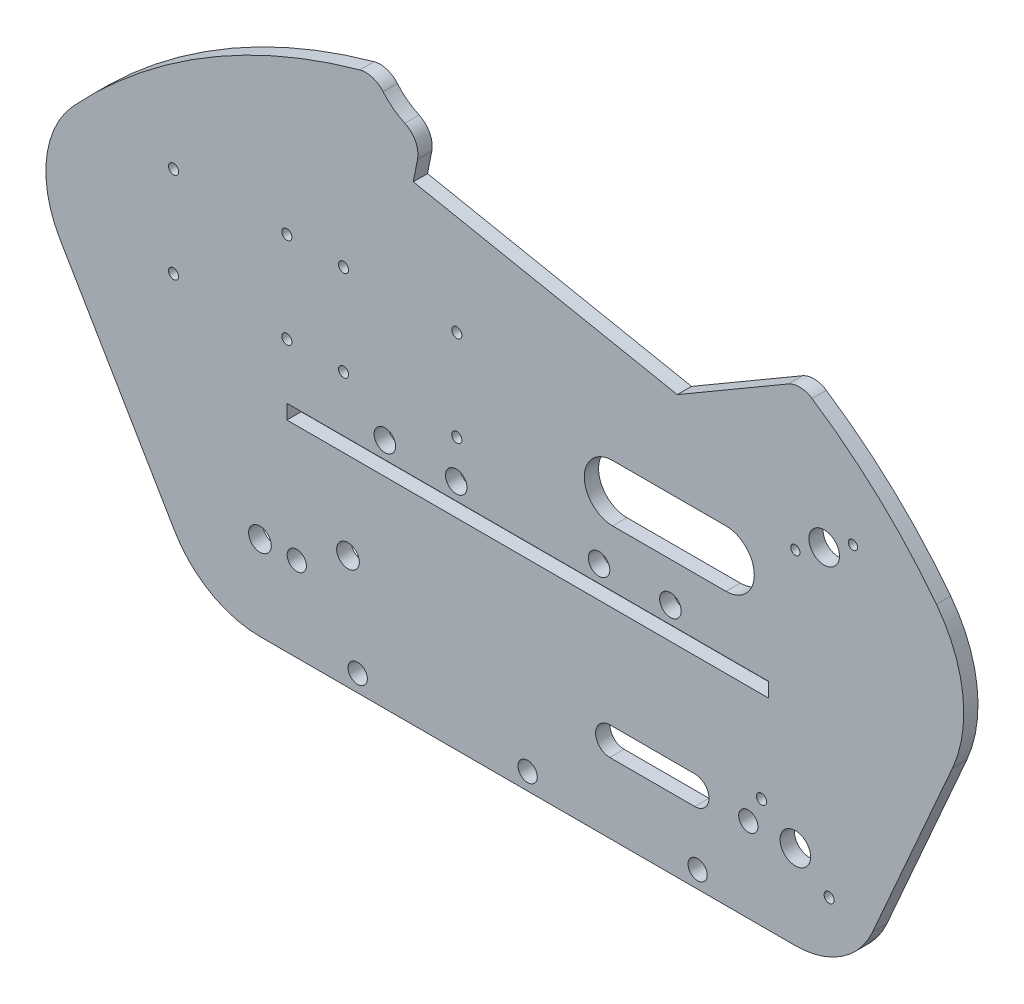
SolidWorks part; units mm, degrees
ref_plane "Front Plane" through (0, 0, 0) normal (0, 0, 1) x (1, 0, 0)
ref_plane "Top Plane" through (0, 0, 0) normal (0, 1, 0) x (1, 0, 0)
ref_plane "Right Plane" through (0, 0, 0) normal (1, 0, 0) x (0, 0, -1)
sketch "Sketch1" plane through (0, 0, 0) normal (0, 0, 1) x (1, 0, 0)
  line L8 (0, 18.9078) -> (120.015, 18.9078) construction
  line L18 (155.2575, 52.1157) -> (-35.2425, 52.1157) construction
  line L37 (0, 0) -> (120.015, 0)
  line L42 (19.7347, 25.5664) -> (0, 18.9078) construction
  line L54 (155.2575, 52.1157) -> (137.3256, 11.3022)
  line L55 (60.0075, 52.1157) -> (60.0075, 18.9078) construction
  line L56 (-35.2425, 52.1157) -> (-17.3106, 11.3022)
  line L59 (151.631, 82.096) -> (-31.616, 82.096) construction
  circle A21 centre (120.015, 18.9078) radius 3.429
  circle A22 centre (0, 18.9078) radius 2.54
  circle A24 centre (19.7347, 25.5664) radius 2.54
  arc A25 (137.3256, 11.3022) -> (120.015, 0) centre (120.015, 18.9078) cw
  arc A26 (0, 0) -> (-17.3106, 11.3022) centre (0, 18.9078) cw
  arc A28 (151.631, 82.096) -> (-31.616, 82.096) centre (60.0075, 11.7572) ccw
  arc A29 (151.631, 82.096) -> (155.2575, 52.1157) centre (128.1135, 64.0417) cw
  arc A30 (-31.616, 82.096) -> (-35.2425, 52.1157) centre (-8.0985, 64.0417) ccw
  dimension "D5" = 18.9078
  dimension "D8" = 29.9803
  dimension "D3" = 52.1157
  dimension "D2" = 6.858
  dimension "D10" = 5.08
  dimension "D1" = 190.5
  dimension "D4" = 18.645
  dimension "D6" = 20.8278
  dimension "D7" = 120.015
  dimension "D9" = 183.2469
extrude "Boss-Extrude1" add sketch "Sketch1" along normal blind 3.2004
sketch "Sketch2" plane through (0, 0, 0) normal (0, 0, -1) x (-1, 0, 0)
  line L14 (-155.2575, 52.1157) -> (35.2425, 52.1157) construction
  line L28 (-92.0115, 52.1157) -> (-76.0095, 52.1157) construction
  line L29 (-76.0095, 52.1157) -> (-44.0055, 52.1157) construction
  line L30 (-44.0055, 52.1157) -> (-28.0035, 52.1157) construction
  circle A0 centre (-92.0115, 52.1157) radius 2.413
  circle A1 centre (-76.0095, 52.1157) radius 2.413
  circle A2 centre (-44.0055, 52.1157) radius 2.413
  circle A3 centre (-28.0035, 52.1157) radius 2.413
  point P11 (-36.0045, 52.1157)
  point P16 (-84.0105, 52.1157)
  dimension "D3" = 4.826
  dimension "D2" = 16.002
  dimension "D4" = 48.006
extrude "Cut-Extrude1" cut sketch "Sketch2" against normal blind 3.2004
sketch "Sketch3" plane through (0, 0, 3.2004) normal (0, 0, 1) x (1, 0, 0)
  line L0 (60.0075, 7.62) -> (60.0075, 0) construction
  line L1 (21.9075, 3.81) -> (98.1075, 3.81) construction
  line L2 (0, 0) -> (120.015, 0) construction
  circle A0 centre (21.9075, 3.81) radius 2.159
  circle A1 centre (60.0075, 3.81) radius 2.159
  circle A2 centre (98.1075, 3.81) radius 2.159
  point P6 (60.0075, 3.81)
  dimension "D3" = 4.318
  dimension "D1" = 76.2
  dimension "D2" = 7.62
extrude "Cut-Extrude2" cut sketch "Sketch3" against normal up to surface (3.2004 mm away) up to face at (89.5985, 52.1157, 0)
sketch "Sketch5" plane through (0, 0, 0) normal (0, 0, -1) x (-1, 0, 0)
  line L0 (-60.0075, 52.1157) -> (-60.0075, 0) construction
  line L1 (-76.0095, 52.1157) -> (-44.0055, 52.1157) construction
  line L3 (0, 0) -> (-120.015, 0) construction
sketch "Sketch6" plane through (0, 0, 0) normal (0, 0, -1) x (-1, 0, 0)
  line L0 (-155.2575, 52.1157) -> (35.2425, 52.1157) construction
  line L1 (-113.9825, 81.3257) -> (-6.0325, 81.3257) construction
  line L2 (-113.9825, 81.3257) -> (-113.9825, 55.9257) construction
  line L3 (-113.9825, 55.9257) -> (-6.0325, 55.9257) construction
  line L4 (-6.0325, 81.3257) -> (-6.0325, 55.9257) construction
  line L5 (-60.0075, 52.1157) -> (-60.0075, 18.9078) construction
  line L6 (-60.0075, 55.9257) -> (-60.0075, 52.1157) construction
  line L7 (-60.0075, 52.1157) -> (-60.0075, 48.3057) construction
  line L9 (-6.0325, 48.3057) -> (-113.9825, 48.3057)
  line L10 (-6.0325, 48.3057) -> (-6.0325, 45.0545)
  line L11 (-6.0325, 45.0545) -> (-113.9825, 45.0545)
  line L12 (-113.9825, 48.3057) -> (-113.9825, 45.0545)
  dimension "D1" = 25.4
  dimension "D2" = 107.95
  dimension "D3" = 3.81
  dimension "D4" = 7.62
  dimension "D5" = 3.2512
extrude "Cut-Extrude3" cut sketch "Sketch6" against normal up to surface (3.2004 mm away) up to face at (24.0665, 3.81, 3.2004)
sketch "Sketch7" plane through (0, 0, 3.2004) normal (0, 0, 1) x (1, 0, 0)
  line L0 (146.2916, 31.7089) -> (111.6995, 46.9073) construction
  line L1 (111.6995, 46.9073) -> (126.4745, 80.5358) construction
  line L3 (137.3256, 11.3022) -> (155.2575, 52.1157) construction
  circle A0 centre (126.4745, 80.5358) radius 3.429
  circle A3 centre (120.015, 18.9078) radius 3.429 construction
  dimension "D1" = 37.7837
  dimension "D2" = 36.7311
extrude "Cut-Extrude4" cut sketch "Sketch7" against normal up to surface (3.2004 mm away) up to face at (60.0075, 46.6801, 0)
sketch "Sketch8" plane through (0, 0, 3.2004) normal (0, 0, 1) x (1, 0, 0)
  line L0 (-32.6149, 80.7753) -> (-17.2714, 56.9367)
  line L1 (-17.2714, 56.9367) -> (38.7942, 93.0228)
  line L2 (38.7942, 93.0228) -> (47.3024, 126.5656)
  line L3 (0, 18.9078) -> (0, 56.9367) construction
  line L4 (0, 56.9367) -> (-17.2714, 56.9367) construction
  line L5 (0, 0) -> (120.015, 0) construction
  arc A0 (151.631, 82.096) -> (-31.616, 82.096) centre (60.0075, 11.7572) ccw construction
  arc A1 (47.3024, 126.5656) -> (-32.6149, 80.7753) centre (60.0075, 11.7572) ccw
  circle A2 centre (0, 18.9078) radius 2.54 construction
  dimension "D1" = 66.675
  dimension "D2" = 137
  dimension "D3" = 28.3497
  dimension "D4" = 38.0289
  dimension "D5" = 17.2714
sketch "Sketch9" plane through (0, 0, 3.2004) normal (0, 0, 1) x (1, 0, 0)
  line L1 (-37.7469, 127.2665) -> (113.9825, 127.2665)
  line L2 (-37.7469, 127.2665) -> (-37.7469, 55.9257)
  line L3 (-37.7469, 55.9257) -> (113.9825, 55.9257)
  line L4 (113.9825, 127.2665) -> (113.9825, 55.9257)
  line L6 (113.9825, 81.3257) -> (113.9825, 55.9257) construction
  line L7 (113.9825, 55.9257) -> (6.0325, 55.9257) construction
  arc A0 (151.631, 82.096) -> (-31.616, 82.096) centre (60.0075, 11.7572) ccw construction
  arc A1 (-31.616, 82.096) -> (-35.2425, 52.1157) centre (-8.0985, 64.0417) ccw construction
sketch "Sketch11" plane through (0, 0, 3.2004) normal (0, 0, 1) x (1, 0, 0)
  line L0 (121.0825, 109.7993) -> (93.5384, 93.7342)
  line L1 (93.5384, 93.7342) -> (34.363, 105.4552)
  line L2 (34.363, 105.4552) -> (38.2746, 125.2036)
  line L6 (113.9825, 48.3057) -> (6.0325, 48.3057) construction
  arc A0 (151.631, 82.096) -> (-31.616, 82.096) centre (60.0075, 11.7572) ccw construction
  arc A1 (38.2746, 125.2036) -> (121.0825, 109.7993) centre (60.0075, 11.7572) cw
  point P4 (0, 0)
  point P5 (0, 0)
  point P6 (0, 0)
  point P7 (0, 0)
  point P10 (0, 0)
  dimension "D1" = 60.325
  dimension "D2" = 20.1321
  dimension "D3" = 11.204
  dimension "D4" = 41.2393
  dimension "D5" = 84.2284
extrude "Cut-Extrude5" cut sketch "Sketch11" against normal up to surface (3.2004 mm away) up to face at (123.0455, 80.5358, 0)
sketch "Sketch12" plane through (0, 0, 3.2004) normal (0, 0, 1) x (1, 0, 0)
  line L2 (35.6411, 114.8543) -> (36.2027, 114.7431)
  line L3 (38.2746, 125.2036) -> (34.363, 105.4552) construction
  line L4 (38.2746, 125.2036) -> (36.2027, 114.7431)
  arc A0 (25.8777, 122.1092) -> (35.6411, 114.8543) centre (38.3949, 128.7574) ccw
  arc A2 (38.2746, 125.2036) -> (-31.616, 82.096) centre (60.0075, 11.7572) ccw construction
  arc A3 (25.8777, 122.1092) -> (38.2746, 125.2036) centre (60.0075, 11.7572) cw
  dimension "D1" = 0.5725
  dimension "D3" = 14.1732
  dimension "D2" = 10.6637
extrude "Cut-Extrude6" cut sketch "Sketch12" against normal up to surface (3.2004 mm away) up to face at (63.7171, 60.738, 0)
sketch "Sketch14" plane through (0, 0, 3.2004) normal (0, 0, 1) x (1, 0, 0)
  line L0 (-44.8116, 54.6857) -> (-19.1425, 10.9597)
  line L1 (0, 0) -> (120.015, 0) construction
  line L2 (-41.8599, 82.0446) -> (25.8777, 122.1092) construction
  line L3 (-41.8599, 82.0446) -> (-44.8116, 54.6857) construction
  line L4 (-9.8103, 145.4597) -> (-9.8103, -20.3847) construction
  arc A0 (25.8777, 122.1092) -> (-41.8599, 82.0446) centre (58.921, -11.052) ccw
  arc A1 (-41.8599, 82.0446) -> (-44.8116, 54.6857) centre (-24.8979, 66.3759) ccw
  arc A4 (-19.1425, 10.9597) -> (0, 0) centre (0, 22.1972) ccw
  arc A5 (25.8777, 122.1092) -> (0, 0) centre (72.988, 48.3288) ccw
  dimension "D2" = 137.1997
  dimension "D4" = 87.5381
  dimension "D5" = 23.0914
  dimension "D1" = 30.415
  dimension "D3" = 78.6991
  dimension "D6" = 27.5176
extrude "Boss-Extrude2" add sketch "Sketch14" against normal up to surface (3.2004 mm away) up to face at (58.8634, 68.0215, 0)
sketch "Sketch13" plane through (0, 0, 3.2004) normal (0, 0, 1) x (1, 0, 0)
  line L0 (44.1325, 81.0717) -> (44.1325, 60.7517) construction
  line L5 (18.7325, 81.0717) -> (18.7325, 60.7517) construction
  line L6 (44.1325, 70.9117) -> (18.7325, 70.9117) construction
  line L7 (6.0325, 81.0717) -> (6.0325, 60.7517) construction
  line L8 (-19.3675, 81.0717) -> (-19.3675, 60.7517) construction
  line L9 (6.0325, 70.9117) -> (-19.3675, 70.9117) construction
  line L10 (113.9825, 48.3057) -> (6.0325, 48.3057) construction
  line L11 (113.9825, 45.0545) -> (113.9825, 48.3057) construction
  circle A0 centre (44.1325, 81.0717) radius 1.1303
  circle A1 centre (44.1325, 60.7517) radius 1.1303
  circle A2 centre (18.7325, 60.7517) radius 1.1303
  circle A3 centre (18.7325, 81.0717) radius 1.1303
  circle A4 centre (6.0325, 81.0717) radius 1.1303
  circle A5 centre (6.0325, 60.7517) radius 1.1303
  circle A6 centre (-19.3675, 60.7517) radius 1.1303
  circle A7 centre (-19.3675, 81.0717) radius 1.1303
  point P13 (31.4325, 70.9117)
  point P22 (-6.6675, 70.9117)
  dimension "D5" = 2.2606
  dimension "D1" = 69.85
  dimension "D2" = 12.7
  dimension "D3" = 25.4
  dimension "D4" = 20.32
  dimension "D6" = 22.606
extrude "Cut-Extrude7" cut sketch "Sketch13" against normal up to surface (3.2004 mm away) up to face at (57.3158, 68.214, 0)
sketch "Sketch15" plane through (0, 0, 3.2004) normal (0, 0, 1) x (1, 0, 0)
  line L0 (113.9825, 48.3057) -> (6.0325, 48.3057) construction
  line L1 (79.0575, 73.7057) -> (104.4575, 73.7057)
  line L2 (79.0575, 73.7057) -> (79.0575, 61.0057) construction
  line L3 (79.0575, 61.0057) -> (104.4575, 61.0057)
  line L4 (104.4575, 73.7057) -> (104.4575, 61.0057) construction
  line L5 (113.9825, 45.0545) -> (113.9825, 48.3057) construction
  line L6 (78.4225, 22.0828) -> (97.4725, 22.0828)
  line L7 (78.4225, 22.0828) -> (78.4225, 15.7328) construction
  line L8 (78.4225, 15.7328) -> (97.4725, 15.7328)
  line L9 (97.4725, 22.0828) -> (97.4725, 15.7328) construction
  line L10 (6.0325, 45.0545) -> (113.9825, 45.0545) construction
  line L11 (97.4725, 18.9078) -> (120.015, 18.9078) construction
  line L12 (0, 0) -> (120.015, 0) construction
  arc A0 (104.4575, 73.7057) -> (104.4575, 61.0057) centre (104.4575, 67.3557) cw
  arc A1 (79.0575, 73.7057) -> (79.0575, 61.0057) centre (79.0575, 67.3557) ccw
  arc A2 (97.4725, 22.0828) -> (97.4725, 15.7328) centre (97.4725, 18.9078) cw
  arc A3 (78.4225, 22.0828) -> (78.4225, 15.7328) centre (78.4225, 18.9078) ccw
  circle A4 centre (120.015, 18.9078) radius 3.429 construction
  circle A5 centre (92.0115, 52.1157) radius 2.413 construction
  dimension "D4" = 8.89
  dimension "D1" = 25.4
  dimension "D2" = 12.7
  dimension "D3" = 12.446
  dimension "D5" = 6.35
  dimension "D6" = 19.05
  dimension "D7" = 16.51
extrude "Cut-Extrude8" cut sketch "Sketch15" against normal up to surface (3.2004 mm away) up to face at (43.0022, 60.7517, 0)
fillet "Fillet1" radius 5.08 3 edges at (121.0825, 109.7993, 1.6002) (36.2027, 114.7431, 1.6002) (25.8777, 122.1092, 1.6002)
sketch "Sketch16" plane through (0, 0, 3.2004) normal (0, 0, 1) x (1, 0, 0)
  line L0 (112.4381, 24.6798) -> (127.5919, 13.1357) construction
  line L1 (0, 0) -> (120.015, 0) construction
  line L2 (120.0293, 76.8147) -> (132.9196, 84.2569) construction
  line L4 (111.6995, 46.9073) -> (126.4745, 80.5358) construction
  circle A0 centre (112.4381, 24.6798) radius 1.1303
  circle A1 centre (127.5919, 13.1357) radius 1.1303
  circle A2 centre (120.0293, 76.8147) radius 1.025
  circle A3 centre (132.9196, 84.2569) radius 1.025
  circle A4 centre (120.015, 18.9078) radius 3.429 construction
  circle A5 centre (126.4745, 80.5358) radius 3.429 construction
  point P10 (120.015, 18.9078)
  point P17 (126.4745, 80.5358)
  dimension "D1" = 2.2606
  dimension "D4" = 2.05
  dimension "D2" = 37.3
  dimension "D3" = 19.05
  dimension "D5" = 14.8844
  dimension "D6" = 36.281
extrude "Cut-Extrude9" cut sketch "Sketch16" against normal up to surface (3.2004 mm away) up to face at (87.9475, 18.9078, 0)
sketch "Sketch20" plane through (0, 0, 3.2004) normal (0, 0, 1) x (1, 0, 0)
  line L0 (8.255, 18.9078) -> (109.4765, 18.9078) construction
  line L1 (60.0075, 18.9078) -> (60.0075, 0) construction
  line L3 (0, 0) -> (120.015, 0) construction
  circle A0 centre (8.255, 18.9078) radius 2.159
  circle A1 centre (109.4765, 18.9078) radius 2.159
  circle A3 centre (0, 18.9078) radius 2.54 construction
  circle A4 centre (120.015, 18.9078) radius 3.429 construction
  dimension "D1" = 4.318
  dimension "D3" = 10.5385
  dimension "D2" = 8.255
  dimension "D4" = 18.9078
extrude "Cut-Extrude11" cut sketch "Sketch20" against normal up to surface (3.2004 mm away) up to face at (111.3078, 24.6798, 0)
